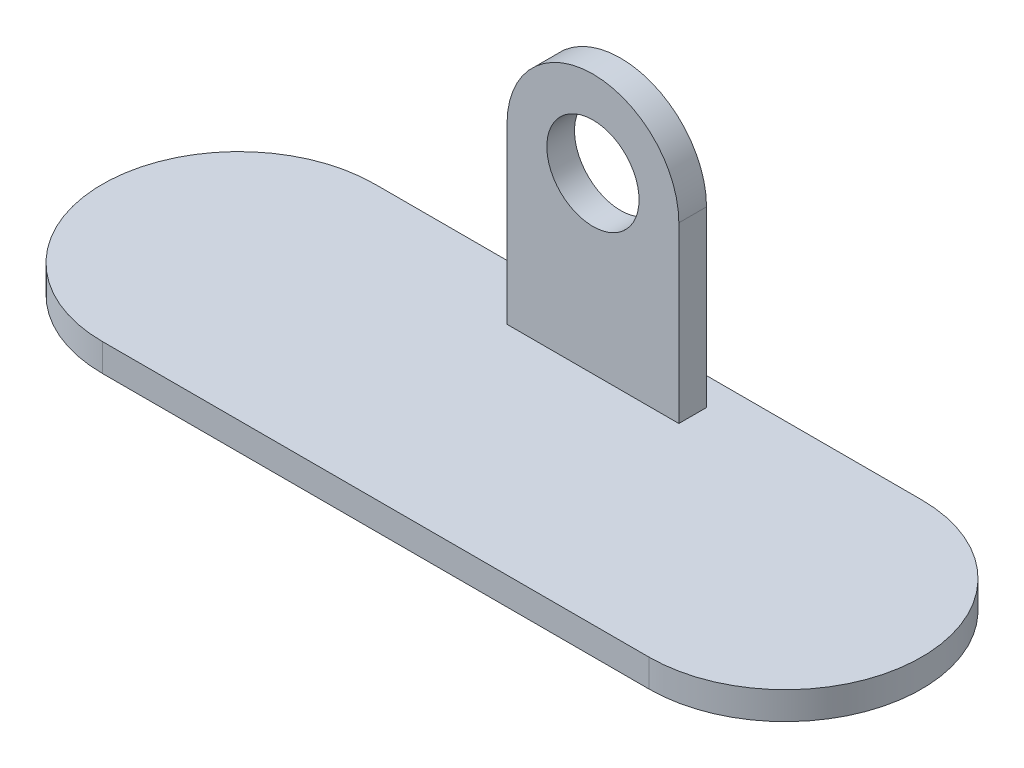
SolidWorks part; units mm, degrees
material "6061 Alloy"
ref_plane "Front Plane" through (0, 0, 0) normal (0, 0, 1) x (1, 0, 0)
ref_plane "Top Plane" through (0, 0, 0) normal (0, 1, 0) x (1, 0, 0)
ref_plane "Right Plane" through (0, 0, 0) normal (1, 0, 0) x (0, 0, -1)
sketch "Sketch1" plane through (0, 0, 0) normal (0, 1, 0) x (1, 0, 0)
  line L0 (-88.9, 0) -> (88.9, 0) construction
  line L1 (-88.9, -44.323) -> (88.9, -44.323)
  line L2 (-88.9, 44.323) -> (88.9, 44.323)
  line L3 (-27.94, 35.323) -> (27.94, 35.323)
  line L4 (0, 0) -> (0, 35.323) construction
  line L5 (-27.94, 35.323) -> (-27.94, 26.323)
  line L6 (-27.94, 26.323) -> (27.94, 26.323)
  line L7 (27.94, 26.323) -> (27.94, 35.323)
  arc A0 (-88.9, 44.323) -> (-88.9, -44.323) centre (-88.9, 0) ccw
  arc A1 (88.9, -44.323) -> (88.9, 44.323) centre (88.9, 0) ccw
  point P8 (0, 0)
  point P14 (0, 35.323)
  dimension "D2" = 88.646
  dimension "D1" = 177.8
  dimension "D3" = 9
  dimension "D4" = 55.88
  dimension "D5" = 9
extrude "Boss-Extrude1" add sketch "Sketch1" along normal blind 9
sketch "Sketch2" plane through (0, 0, -35.323) normal (0, 0, 1) x (1, 0, 0)
  line L0 (-27.94, 0) -> (27.94, 0)
  line L1 (27.94, 0) -> (27.94, 65.532)
  line L3 (-27.94, 65.532) -> (-27.94, 0)
  arc A0 (27.94, 65.532) -> (-27.94, 65.532) centre (0, 65.532) ccw
  circle A1 centre (0, 65.532) radius 15
  dimension "D2" = 30
  dimension "D1" = 65.532
extrude "Boss-Extrude2" add sketch "Sketch2" along normal blind 9
